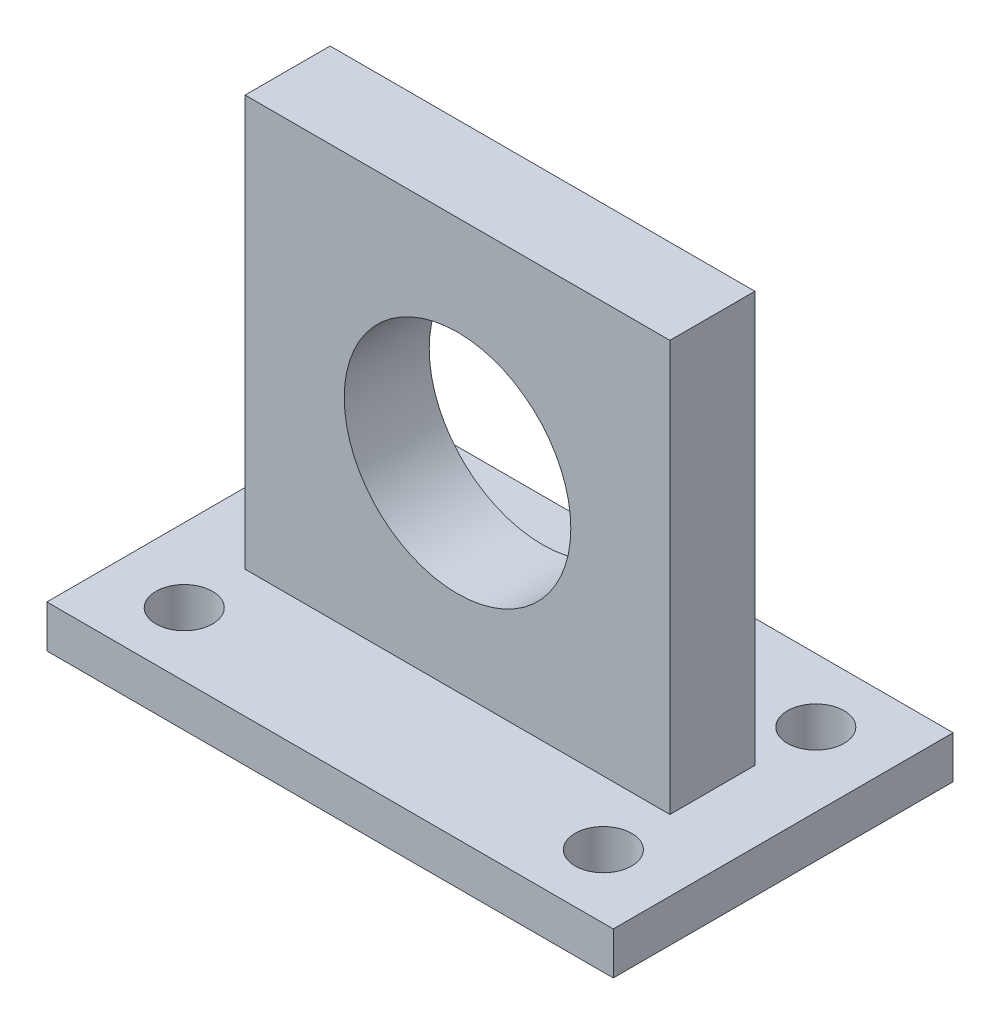
SolidWorks part; units mm, degrees
ref_plane "Front" through (0, 0, 0) normal (0, 0, 1) x (1, 0, 0)
ref_plane "Top" through (0, 0, 0) normal (0, 1, 0) x (1, 0, 0)
ref_plane "Right" through (0, 0, 0) normal (1, 0, 0) x (0, 0, -1)
sketch "草图1" plane through (0, 0, 0) normal (0, 1, 0) x (1, 0, 0)
  line L0 (0, 0) -> (0, 12) construction
  line L1 (0, 0) -> (20, 0) construction
  line L2 (-20, 12) -> (20, 12)
  line L3 (20, 12) -> (20, -12)
  line L4 (-20, 12) -> (-20, -12)
  line L5 (-20, -12) -> (20, -12)
  line L6 (0, 0) -> (0, -7.5) construction
  line L7 (0, -7.5) -> (-14.8, -7.5) construction
  circle A0 centre (-14.8, -7.5) radius 2
  circle A1 centre (14.8, -7.5) radius 2
  circle A2 centre (-14.8, 7.5) radius 2
  circle A3 centre (14.8, 7.5) radius 2
  point P9 (-20, 0)
extrude "凸台-拉伸1" add sketch "草图1" along normal blind 3
sketch "草图2" plane through (0, 3, 0) normal (0, 1, 0) x (1, 0, 0)
  line L0 (0, 0) -> (0, 3) construction
  line L1 (0, 3) -> (20, 3) construction
  line L2 (20, -12) -> (20, 12) construction
  line L3 (20, 3) -> (20, -3) construction
  line L10 (0, 0) -> (0, -3) construction
  line L11 (0, -3) -> (-10, -3) construction
  line L12 (-10, -3) -> (-10, 3) construction
  line L14 (-10, 3) -> (-10, -3)
  line L15 (-10, -3) -> (10, -3)
  line L17 (-10, 3) -> (10, 3)
  line L18 (10, 3) -> (10, -3)
extrude "凸台-拉伸2" add sketch "草图2" along normal blind 25
sketch "草图3" plane through (0, 0, 3) normal (0, 0, 1) x (1, 0, 0)
  line L0 (0, 3) -> (0, 17) construction
  line L1 (-20, 3) -> (20, 3) construction
  circle A1 centre (0, 17) radius 7.9375
extrude "切除-拉伸1" cut sketch "草图3" against normal blind 10
sketch "草图4" plane through (0, 0, 3) normal (0, 0, 1) x (1, 0, 0)
  line L0 (0, 17) -> (15, 17) construction
  line L1 (15, 17) -> (15, 32) construction
  line L2 (15, 32) -> (-15, 32) construction
  line L3 (-15, 32) -> (-15, 3) construction
  line L4 (-20, 3) -> (20, 3) construction
  line L5 (-15, 32) -> (-15, 3)
  line L6 (-15, 3) -> (-10, 3)
  line L7 (-10, 3) -> (-10, 28)
  line L8 (-10, 28) -> (10, 28)
  line L10 (-15, 32) -> (15, 32)
  line L12 (15, 3) -> (10, 3)
  line L13 (10, 3) -> (10, 28)
  line L14 (15, 32) -> (15, 3)
extrude "凸台-拉伸4" add sketch "草图4" against normal blind 6
sketch "草图5" plane through (0, 0, 3) normal (0, 0, 1) x (1, 0, 0)
  circle A0 centre (0, 17) radius 8
extrude "切除-拉伸2" cut sketch "草图5" against normal blind 6
